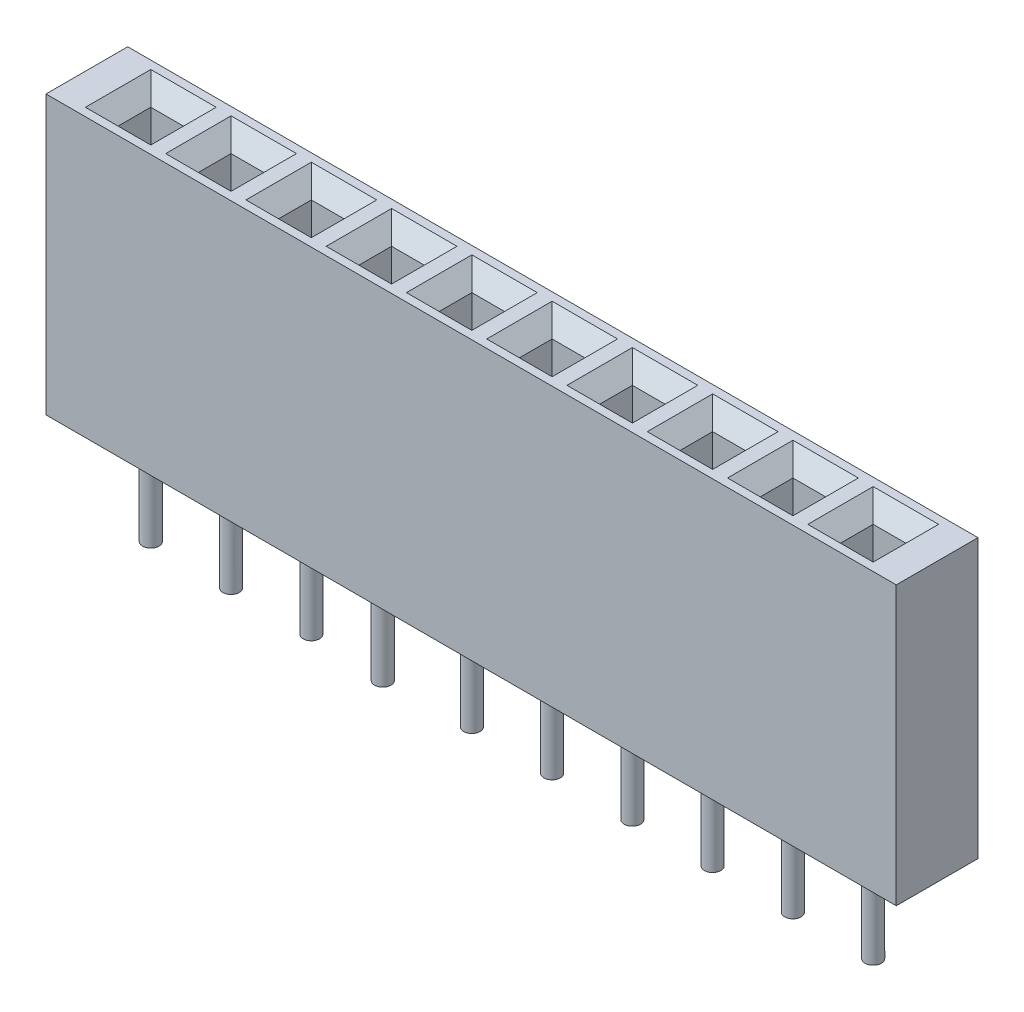
SolidWorks part; units mm, degrees
ref_plane "Front" through (0, 0, 0) normal (0, 0, 1) x (1, 0, 0)
ref_plane "Top" through (0, 0, 0) normal (0, 1, 0) x (1, 0, 0)
ref_plane "Right" through (0, 0, 0) normal (1, 0, 0) x (0, 0, -1)
sketch "Sketch1" plane through (0, 0, 0) normal (0, 1, 0) x (1, 0, 0)
  line L1 (0, 0) -> (26, 0)
  line L2 (0, 0) -> (0, 2.5)
  line L3 (0, 2.5) -> (26, 2.5)
  line L4 (26, 0) -> (26, 2.5)
  dimension "D1" = 2.5
  dimension "D2" = 26
extrude "Boss-Extrude1" add sketch "Sketch1" along normal blind 8.5
sketch "Sketch2" plane through (0, 8.5, 0) normal (0, 1, 0) x (1, 0, 0)
  line L0 (0, 2.5) -> (0, 0) construction
  line L1 (1.4545, 1.75) -> (2.4545, 1.75)
  line L2 (1.4545, 1.75) -> (1.4545, 0.75)
  line L3 (1.4545, 0.75) -> (2.4545, 0.75)
  line L4 (2.4545, 1.75) -> (2.4545, 0.75)
  line L5 (0, 1.25) -> (26, 1.25) construction
  line L6 (26, 0) -> (26, 2.5) construction
  line L8 (3.909, 1.75) -> (4.909, 1.75)
  line L9 (3.909, 1.75) -> (3.909, 0.75)
  line L10 (3.909, 0.75) -> (4.909, 0.75)
  line L11 (4.909, 1.75) -> (4.909, 0.75)
  line L12 (6.3635, 1.75) -> (7.3635, 1.75)
  line L13 (6.3635, 1.75) -> (6.3635, 0.75)
  line L14 (6.3635, 0.75) -> (7.3635, 0.75)
  line L15 (7.3635, 1.75) -> (7.3635, 0.75)
  line L16 (8.818, 1.75) -> (9.818, 1.75)
  line L17 (8.818, 1.75) -> (8.818, 0.75)
  line L18 (8.818, 0.75) -> (9.818, 0.75)
  line L19 (9.818, 1.75) -> (9.818, 0.75)
  line L20 (11.2725, 1.75) -> (12.2725, 1.75)
  line L21 (11.2725, 1.75) -> (11.2725, 0.75)
  line L22 (11.2725, 0.75) -> (12.2725, 0.75)
  line L23 (12.2725, 1.75) -> (12.2725, 0.75)
  line L24 (13.727, 1.75) -> (14.727, 1.75)
  line L25 (13.727, 1.75) -> (13.727, 0.75)
  line L26 (13.727, 0.75) -> (14.727, 0.75)
  line L27 (14.727, 1.75) -> (14.727, 0.75)
  line L28 (16.1815, 1.75) -> (17.1815, 1.75)
  line L29 (16.1815, 1.75) -> (16.1815, 0.75)
  line L30 (16.1815, 0.75) -> (17.1815, 0.75)
  line L31 (17.1815, 1.75) -> (17.1815, 0.75)
  line L32 (18.636, 1.75) -> (19.636, 1.75)
  line L33 (18.636, 1.75) -> (18.636, 0.75)
  line L34 (18.636, 0.75) -> (19.636, 0.75)
  line L35 (19.636, 1.75) -> (19.636, 0.75)
  line L36 (21.0905, 1.75) -> (22.0905, 1.75)
  line L37 (21.0905, 1.75) -> (21.0905, 0.75)
  line L38 (21.0905, 0.75) -> (22.0905, 0.75)
  line L39 (22.0905, 1.75) -> (22.0905, 0.75)
  line L40 (23.545, 1.75) -> (24.545, 1.75)
  line L41 (23.545, 1.75) -> (23.545, 0.75)
  line L42 (23.545, 0.75) -> (24.545, 0.75)
  line L43 (24.545, 1.75) -> (24.545, 0.75)
  dimension "D1" = 1
  dimension "D2" = 1.4545
  dimension "D3" = 1
  dimension "D4" = 1.4545
  dimension "D5" = 1.4545
  dimension "D6" = 1.4545
  dimension "D7" = 1.4545
  dimension "D8" = 1.4545
  dimension "D9" = 1.4545
  dimension "D10" = 1.4545
  dimension "D11" = 1.4545
  dimension "D12" = 1.4545
extrude "Cut-Extrude1" cut sketch "Sketch2" against normal blind 5
chamfer "Chamfer1" distance 0.5 angle 45 40 edges at (24.545, 8.5, -1.25) (24.045, 8.5, -1.75) (23.545, 8.5, -1.25) (24.045, 8.5, -0.75) (22.0905, 8.5, -1.25) (21.5905, 8.5, -1.75) (21.0905, 8.5, -1.25) (21.5905, 8.5, -0.75) (19.636, 8.5, -1.25) (19.136, 8.5, -1.75) (18.636, 8.5, -1.25) (19.136, 8.5, -0.75) (17.1815, 8.5, -1.25) (16.6815, 8.5, -1.75) (16.1815, 8.5, -1.25) (16.6815, 8.5, -0.75) (14.727, 8.5, -1.25) (14.227, 8.5, -1.75) (13.727, 8.5, -1.25) (14.227, 8.5, -0.75) (12.2725, 8.5, -1.25) (11.7725, 8.5, -1.75) (11.2725, 8.5, -1.25) (11.7725, 8.5, -0.75) (9.818, 8.5, -1.25) (9.318, 8.5, -1.75) (8.818, 8.5, -1.25) (9.318, 8.5, -0.75) (7.3635, 8.5, -1.25) (6.8635, 8.5, -1.75) (6.3635, 8.5, -1.25) (6.8635, 8.5, -0.75) (4.909, 8.5, -1.25) (4.409, 8.5, -1.75) (3.909, 8.5, -1.25) (4.409, 8.5, -0.75) (2.4545, 8.5, -1.25) (1.9545, 8.5, -1.75) (1.4545, 8.5, -1.25) (1.9545, 8.5, -0.75)
sketch "Sketch3" plane through (0, 3.5, 0) normal (0, 1, 0) x (1, 0, 0)
  line L0 (1.4545, 0.75) -> (2.4545, 1.75) construction
  line L1 (3.909, 0.75) -> (4.909, 1.75) construction
  line L2 (6.3635, 0.75) -> (7.3635, 1.75) construction
  line L3 (8.818, 0.75) -> (9.818, 1.75) construction
  line L4 (11.2725, 0.75) -> (12.2725, 1.75) construction
  line L5 (13.727, 0.75) -> (14.727, 1.75) construction
  line L6 (16.1815, 0.75) -> (17.1815, 1.75) construction
  line L7 (18.636, 0.75) -> (19.636, 1.75) construction
  line L8 (21.0905, 0.75) -> (22.0905, 1.75) construction
  line L9 (23.545, 0.75) -> (24.545, 1.75) construction
  circle A0 centre (1.9545, 1.25) radius 0.25
  circle A1 centre (4.409, 1.25) radius 0.25
  circle A2 centre (6.8635, 1.25) radius 0.25
  circle A3 centre (9.1833, 1.1153) radius 0.25
  circle A4 centre (11.7725, 1.25) radius 0.25
  circle A5 centre (14.227, 1.25) radius 0.25
  circle A6 centre (16.6815, 1.25) radius 0.25
  circle A7 centre (19.136, 1.25) radius 0.25
  circle A8 centre (21.5905, 1.25) radius 0.25
  circle A9 centre (24.045, 1.25) radius 0.25
  dimension "D1" = 0.5
extrude "Boss-Extrude2" add sketch "Sketch3" against normal blind 6.5
